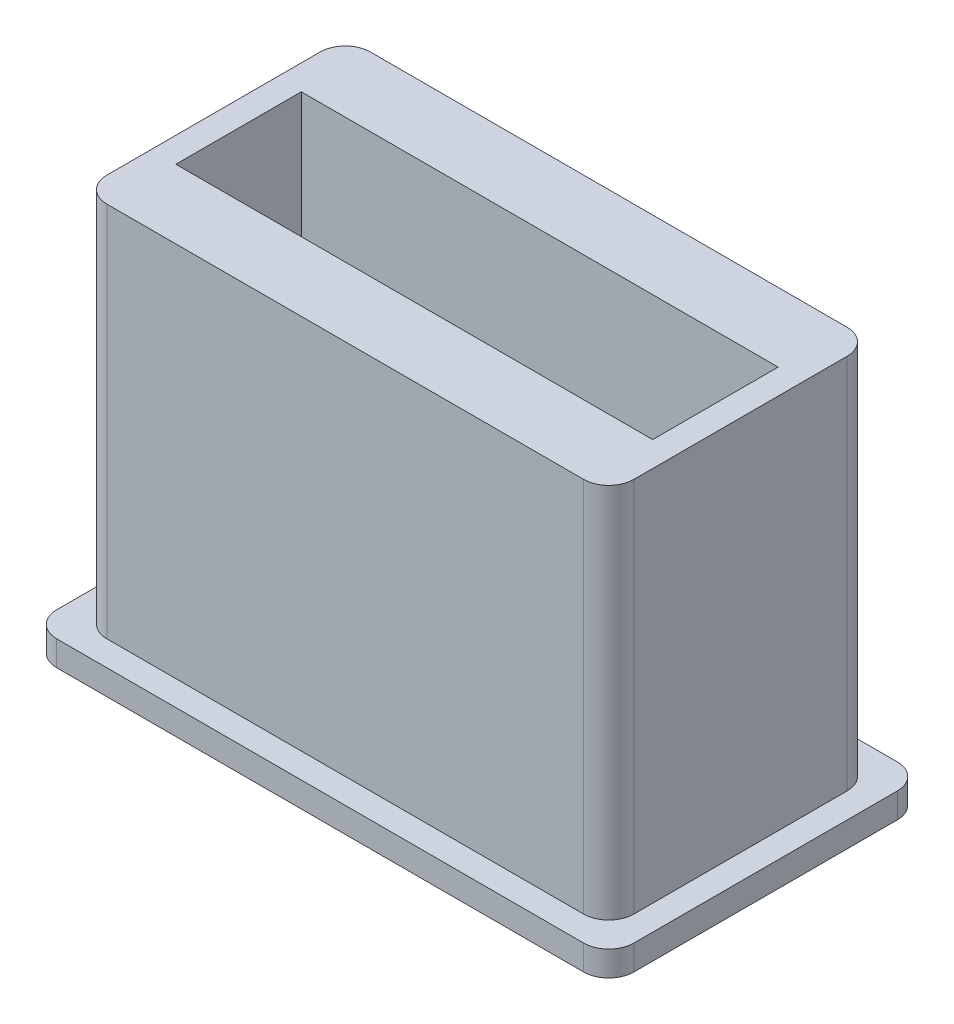
SolidWorks part; units mm, degrees
ref_plane "Front Plane" through (0, 0, 0) normal (0, 0, 1) x (1, 0, 0)
ref_plane "Top Plane" through (0, 0, 0) normal (0, 1, 0) x (1, 0, 0)
ref_plane "Right Plane" through (0, 0, 0) normal (1, 0, 0) x (0, 0, -1)
sketch "Sketch2" plane through (0, 0, 0) normal (0, 1, 0) x (1, 0, 0)
  line L1 (95, -25) -> (-95, -25)
  line L2 (95, -25) -> (95, 25)
  line L3 (95, 25) -> (-95, 25)
  line L4 (-95, -25) -> (-95, 25)
  line L5 (95, -25) -> (-95, 25) construction
  line L6 (95, 25) -> (-95, -25) construction
  line L7 (105, -52.5) -> (-105, -52.5)
  line L8 (105, -52.5) -> (105, 52.5)
  line L9 (105, 52.5) -> (-105, 52.5)
  line L10 (-105, -52.5) -> (-105, 52.5)
  line L11 (105, -52.5) -> (-105, 52.5) construction
  line L12 (105, 52.5) -> (-105, -52.5) construction
  point P0 (0, 0)
  point P7 (0, 0)
  dimension "D1" = 190
  dimension "D2" = 50
  dimension "D3" = 210
  dimension "D4" = 105
extrude "Boss-Extrude2" add sketch "Sketch2" along normal blind 150
fillet "Fillet1" radius 10 1 edges at (-105, 75, -52.5)
fillet "Fillet2" radius 10 1 edges at (-105, 75, 52.5)
fillet "Fillet3" radius 10 1 edges at (105, 75, 52.5)
fillet "Fillet4" radius 10 1 edges at (105, 75, -52.5)
sketch "Sketch3" plane through (-105, 0, 0) normal (-1, 0, 0) x (0, 0, 1)
  line L0 (0, 150) -> (0, 0) construction
  line L1 (-42.5, 150) -> (42.5, 150) construction
  circle A0 centre (0, 75) radius 16.1
  dimension "D1" = 32.2
extrude "Cut-Extrude1" cut sketch "Sketch3" against normal blind 10 contours A0
sketch "Sketch4" plane through (0, 0, 0) normal (0, 1, 0) x (1, 0, 0)
  line L1 (115, -62.5) -> (-115, -62.5)
  line L2 (115, -62.5) -> (115, 62.5)
  line L3 (115, 62.5) -> (-115, 62.5)
  line L4 (-115, -62.5) -> (-115, 62.5)
  line L5 (115, -62.5) -> (-115, 62.5) construction
  line L6 (115, 62.5) -> (-115, -62.5) construction
  point P0 (0, 0)
  dimension "D1" = 230
  dimension "D2" = 125
extrude "Boss-Extrude3" add sketch "Sketch4" against normal blind 10
fillet "Fillet5" radius 10 1 edges at (115, -5, 62.5)
fillet "Fillet6" radius 10 1 edges at (115, -5, -62.5)
fillet "Fillet7" radius 10 1 edges at (-115, -5, -62.5)
fillet "Fillet8" radius 10 1 edges at (-115, -5, 62.5)
sketch "Sketch7" plane through (0, 0, 0) normal (0, 1, 0) x (1, 0, 0)
  line L1 (-5, 25) -> (5, 25)
  line L2 (-5, 25) -> (-5, -25)
  line L3 (-5, -25) -> (5, -25)
  line L4 (5, 25) -> (5, -25)
  line L5 (-5, 25) -> (5, -25) construction
  line L6 (-5, -25) -> (5, 25) construction
  point P0 (0, 0)
  dimension "D1" = 50
  dimension "D2" = 10
extrude "Boss-Extrude4" add sketch "Sketch7" along normal blind 75
sketch "Sketch8" plane through (-5, 0, 0) normal (-1, 0, 0) x (0, 0, 1)
  line L0 (-25, 75) -> (25, 75) construction
  circle A0 centre (0, 75) radius 16.1
  dimension "D1" = 32.2
extrude "Cut-Extrude2" cut sketch "Sketch8" against normal blind 10 contours A0
